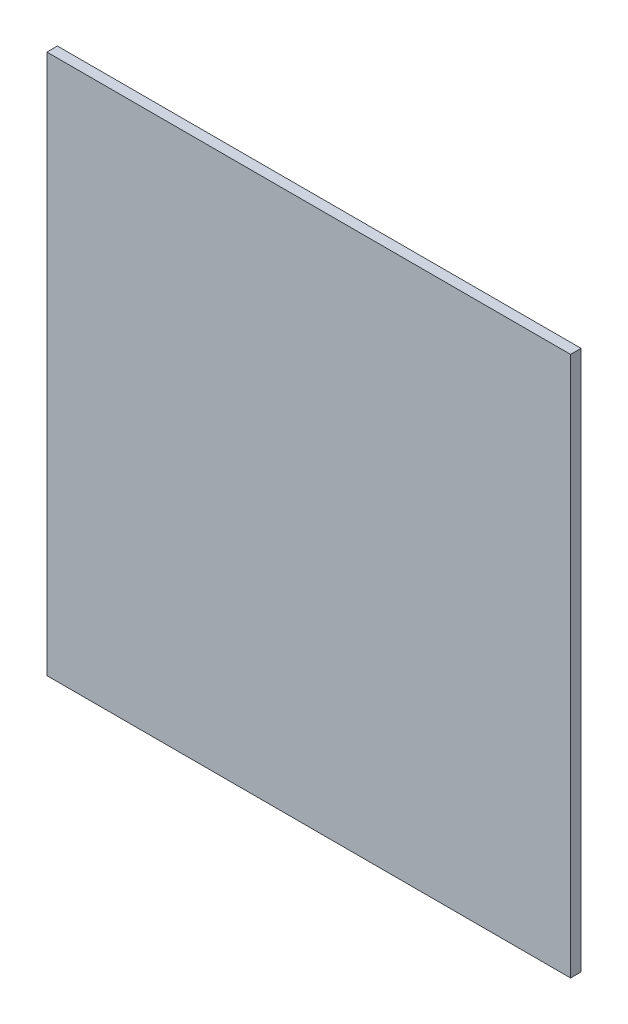
SolidWorks part; units mm, degrees
ref_plane "Front Plane" through (0, 0, 0) normal (0, 0, 1) x (1, 0, 0)
ref_plane "Top Plane" through (0, 0, 0) normal (0, 1, 0) x (1, 0, 0)
ref_plane "Right Plane" through (0, 0, 0) normal (1, 0, 0) x (0, 0, -1)
sketch "Sketch1" plane through (0, 0, 0) normal (0, 0, 1) x (1, 0, 0)
  line L0 (62.1, -257.4) -> (51.7484, -257.4) construction
  line L1 (0, 0) -> (249.6, 0)
  line L2 (0, 0) -> (0, -257.4)
  line L3 (0, -257.4) -> (249.6, -257.4)
  line L4 (249.6, 0) -> (249.6, -257.4)
  dimension "D2" = 249.6
extrude "Boss-Extrude1" add sketch "Sketch1" along normal blind 5
